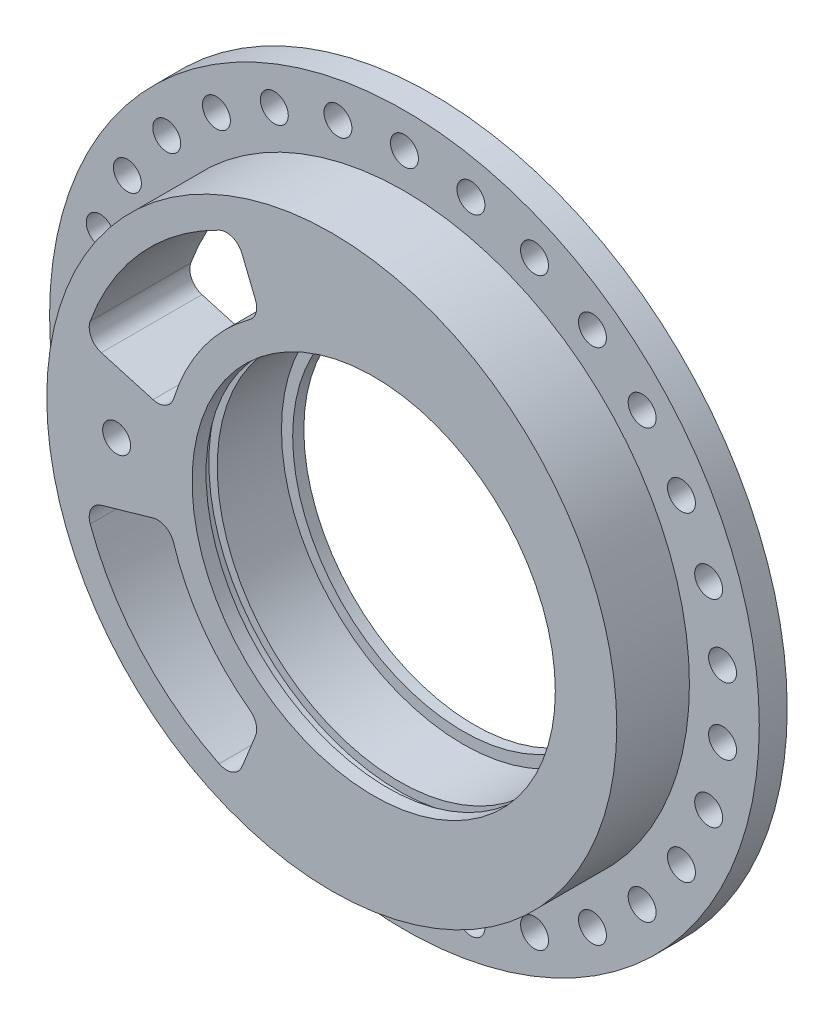
SolidWorks part; units mm, degrees
ref_plane "Front Plane" through (0, 0, 0) normal (0, 0, 1) x (1, 0, 0)
ref_plane "Top Plane" through (0, 0, 0) normal (0, 1, 0) x (1, 0, 0)
ref_plane "Right Plane" through (0, 0, 0) normal (1, 0, 0) x (0, 0, -1)
sketch "Sketch1" plane through (0, 0, 0) normal (0, 0, 1) x (1, 0, 0)
  circle A0 centre (0, 0) radius 63.5
  dimension "D1" = 127
extrude "Boss-Extrude1" add sketch "Sketch1" along normal blind 5
sketch "Sketch2" plane through (0, 0, 5) normal (0, 0, 1) x (1, 0, 0)
  circle A0 centre (0, 0) radius 51
  dimension "D1" = 102
extrude "Boss-Extrude2" add sketch "Sketch2" along normal blind 13
sketch "Sketch3" plane through (0, 0, 18) normal (0, 0, 1) x (1, 0, 0)
  circle A0 centre (7.5, 0) radius 32.5
  dimension "D1" = 65
  dimension "D2" = 7.5
extrude "Cut-Extrude1" cut sketch "Sketch3" against normal through all
sketch "Sketch4" plane through (0, 0, 18) normal (0, 0, 1) x (1, 0, 0)
  circle A0 centre (7.5, 0) radius 32.5
  circle A1 centre (7.5, 0) radius 34
  dimension "D1" = 68
extrude "Cut-Extrude9" cut sketch "Sketch4" against normal blind 2 from offset 2.5 offset against normal yes
sketch "Sketch6" plane through (0, 0, 0) normal (0, 0, -1) x (-1, 0, 0)
  circle A0 centre (-7.5, 0) radius 30.5
  circle A1 centre (-7.5, 0) radius 32.5
  dimension "D1" = 61
extrude "Boss-Extrude3" add sketch "Sketch6" against normal blind 2
sketch "Sketch7" plane through (0, 0, 18) normal (0, 0, 1) x (1, 0, 0)
  circle A1 centre (0, 57.24) radius 2.5
  circle A2 centre (11.9009, 55.9892) radius 2.5
  circle A3 centre (23.2816, 52.2913) radius 2.5
  circle A4 centre (33.6448, 46.3081) radius 2.5
  circle A5 centre (42.5376, 38.301) radius 2.5
  circle A6 centre (49.5713, 28.62) radius 2.5
  circle A7 centre (54.4385, 17.6881) radius 2.5
  circle A8 centre (56.9264, 5.9832) radius 2.5
  circle A9 centre (56.9264, -5.9832) radius 2.5
  circle A10 centre (54.4385, -17.6881) radius 2.5
  circle A11 centre (49.5713, -28.62) radius 2.5
  circle A12 centre (42.5376, -38.301) radius 2.5
  circle A13 centre (33.6448, -46.3081) radius 2.5
  circle A14 centre (23.2816, -52.2913) radius 2.5
  circle A15 centre (11.9009, -55.9892) radius 2.5
  circle A16 centre (0, -57.24) radius 2.5
  circle A17 centre (-11.9009, -55.9892) radius 2.5
  circle A18 centre (-23.2816, -52.2913) radius 2.5
  circle A19 centre (-33.6448, -46.3081) radius 2.5
  circle A20 centre (-42.5376, -38.301) radius 2.5
  circle A21 centre (-49.5713, -28.62) radius 2.5
  circle A22 centre (-54.4385, -17.6881) radius 2.5
  circle A23 centre (-56.9264, -5.9832) radius 2.5
  circle A24 centre (-56.9264, 5.9832) radius 2.5
  circle A25 centre (-54.4385, 17.6881) radius 2.5
  circle A26 centre (-49.5713, 28.62) radius 2.5
  circle A27 centre (-42.5376, 38.301) radius 2.5
  circle A28 centre (-33.6448, 46.3081) radius 2.5
  circle A29 centre (-23.2816, 52.2913) radius 2.5
  circle A30 centre (-11.9009, 55.9892) radius 2.5
  dimension "D2" = 5
  dimension "D3" = 30
extrude "Cut-Extrude10" cut sketch "Sketch7" against normal through all
sketch "Sketch9" plane through (0, 0, 18) normal (0, 0, 1) x (1, 0, 0)
  circle A0 centre (-38.5, 0) radius 2.5
  circle A1 centre (7.5, 0) radius 32.5 construction
  dimension "D2" = 5
  dimension "D1" = 46
extrude "Cut-Extrude11" cut sketch "Sketch9" against normal through all
sketch "Sketch10" plane through (0, 0, 18) normal (0, 0, 1) x (1, 0, 0)
  line L1 (-12.7516, 31.5614) -> (-17.2319, 42.6505)
  line L2 (-29.0623, 8.3335) -> (-44.218, 12.6793)
  line L3 (9.9, 0) -> (-9.9, 0) construction
  line L4 (-12.7516, -31.5614) -> (-17.2319, -42.6505)
  line L5 (-29.0623, -8.3335) -> (-44.218, -12.6793)
  arc A0 (-17.2319, 42.6505) -> (-44.218, 12.6793) centre (0, 0) ccw
  arc A2 (-12.7516, 31.5614) -> (-29.0623, 8.3335) centre (7.5, 0) ccw
  arc A3 (-12.7516, -31.5614) -> (-29.0623, -8.3335) centre (7.5, 0) cw
  arc A4 (-17.2319, -42.6505) -> (-44.218, -12.6793) centre (0, 0) cw
  dimension "D1" = 92
  dimension "D2" = 75
extrude "Cut-Extrude12" cut sketch "Sketch10" against normal through all
fillet "Fillet1" radius 3 8 edges at (-12.7516, -31.5614, 9) (-17.2319, -42.6505, 9) (-29.0623, -8.3335, 9) (-44.218, -12.6793, 9) (-17.2319, 42.6505, 9) (-29.0623, 8.3335, 9) (-12.7516, 31.5614, 9) (-44.218, 12.6793, 9)
